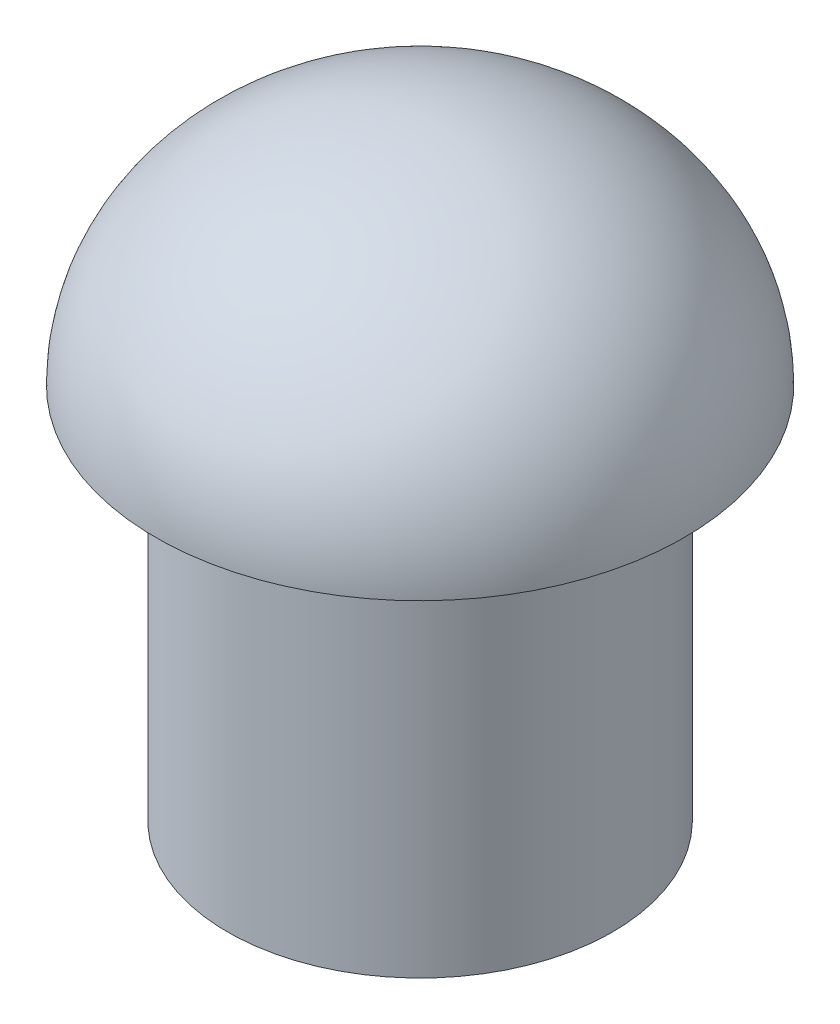
SolidWorks part; units mm, degrees
ref_plane "Front Plane" through (0, 0, 0) normal (0, 0, 1) x (1, 0, 0)
ref_plane "Top Plane" through (0, 0, 0) normal (0, 1, 0) x (1, 0, 0)
ref_plane "Right Plane" through (0, 0, 0) normal (1, 0, 0) x (0, 0, -1)
sketch "Sketch1" plane through (0, 0, 0) normal (1, 0, 0) x (0, 0, -1)
  line L1 (0, 0) -> (3.5, 0)
  line L2 (0, 0) -> (0, 3)
  ellipse E0 centre (0, 0) end of major axis (-3.5, 0) minor radius 3 (3.5, 0) -> (0, 3) ccw
  dimension "D1" = 3.5
  dimension "D2" = 3
ref_axis "Axis1" through (0, 0, 0) along (0, 1, 0)
revolve "Revolve5" add sketch "Sketch1" angle 360 about axis through (0, 0, 0) along (0, 1, 0)
sketch "Sketch3" plane through (0, 0, 0) normal (0, -1, 0) x (1, 0, 0)
  line L1 (-1.8031, -1.8031) -> (1.8031, -1.8031) construction
  line L2 (-1.8031, -1.8031) -> (-1.8031, 1.8031) construction
  line L3 (-1.8031, 1.8031) -> (1.8031, 1.8031) construction
  line L4 (1.8031, -1.8031) -> (1.8031, 1.8031) construction
  line L5 (-1.8031, -1.8031) -> (1.8031, 1.8031) construction
  line L6 (-1.8031, 1.8031) -> (1.8031, -1.8031) construction
  circle A0 centre (0, 0) radius 2.55
  point P0 (0, 0)
  dimension "D1" = 5.1
extrude "Boss-Extrude1" add sketch "Sketch3" along normal blind 5
sketch "Sketch4" plane through (0, -5, 0) normal (0, -1, 0) x (1, 0, 0)
  line L1 (-1.55, -1.55) -> (1.55, -1.55)
  line L2 (-1.55, -1.55) -> (-1.55, 1.55)
  line L3 (-1.55, 1.55) -> (1.55, 1.55)
  line L4 (1.55, -1.55) -> (1.55, 1.55)
  line L5 (-1.55, -1.55) -> (1.55, 1.55) construction
  line L6 (-1.55, 1.55) -> (1.55, -1.55) construction
  point P0 (0, 0)
  dimension "D1" = 3.1
extrude "Cut-Extrude1" cut sketch "Sketch4" against normal blind 2
